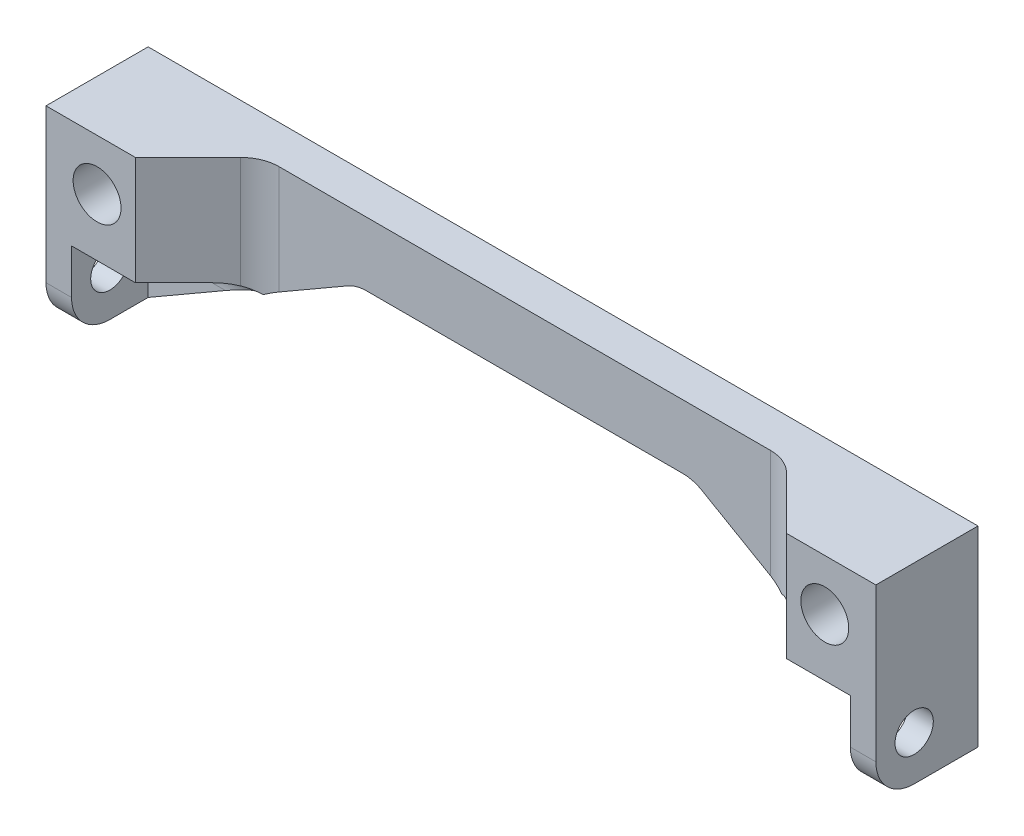
SolidWorks part; units mm, degrees
ref_plane "Front Plane" through (0, 0, 0) normal (0, 0, 1) x (1, 0, 0)
ref_plane "Top Plane" through (0, 0, 0) normal (0, 1, 0) x (1, 0, 0)
ref_plane "Right Plane" through (0, 0, 0) normal (1, 0, 0) x (0, 0, -1)
sketch "Sketch2" plane through (0, 0, 0) normal (0, 0, 1) x (1, 0, 0)
  line L0 (-65, 0) -> (65, 0)
  line L1 (65, 0) -> (65, -30)
  line L2 (65, -30) -> (61, -30)
  line L3 (61, -30) -> (26.359, -10)
  line L4 (26.359, -10) -> (-26.359, -10)
  line L5 (-26.359, -10) -> (-61, -30)
  line L6 (-61, -30) -> (-65, -30)
  line L7 (-65, -30) -> (-65, 0)
  circle A0 centre (-57, -8) radius 3.75
  circle A1 centre (57, -8) radius 3.75
  dimension "D6" = 7.5
  dimension "D1" = 30
  dimension "D2" = 130
  dimension "D3" = 4
  dimension "D4" = 10
  dimension "D5" = 30
  dimension "D7" = 8
  dimension "D8" = 8
  dimension "D9" = 8
  dimension "D10" = 30
extrude "Boss-Extrude1" add sketch "Sketch2" along normal blind 16
sketch "Sketch3" plane through (65, 0, 0) normal (1, 0, 0) x (0, 0, -1)
  line L0 (0, -30) -> (0, 0) construction
  line L1 (-16, -30) -> (0, -30) construction
  circle A0 centre (-10, -23) radius 3
  dimension "D2" = 6
  dimension "D1" = 7
  dimension "D3" = 10
extrude "Cut-Extrude1" cut sketch "Sketch3" against normal through all
sketch "Sketch4" plane through (0, 0, 0) normal (0, 1, 0) x (1, 0, 0)
  line L0 (-51, -16) -> (-41, -6)
  line L1 (65, -16) -> (-65, -16) construction
  line L2 (-41, -6) -> (41, -6)
  line L3 (41, -6) -> (51, -16)
  line L4 (51, -16) -> (-51, -16)
  line L5 (-65, -16) -> (-65, 0) construction
  line L6 (65, -16) -> (65, 0) construction
  line L7 (65, 0) -> (-65, 0) construction
  dimension "D1" = 14
  dimension "D2" = 14
  dimension "D3" = 6
  dimension "D4" = 45
extrude "Cut-Extrude2" cut sketch "Sketch4" against normal through all
sketch "Sketch5" plane through (-65, 0, 0) normal (-1, 0, 0) x (0, 0, 1)
  line L0 (4, -23) -> (4, -30)
  line L1 (16, -30) -> (0, -30) construction
  line L2 (4, -30) -> (16, -30)
  line L3 (16, -30) -> (16, -17)
  line L4 (16, 0) -> (16, -30) construction
  line L5 (16, -17) -> (10, -17)
  arc A0 (10, -17) -> (4, -23) centre (10, -23) ccw
  dimension "D1" = 12
extrude "Cut-Extrude3" cut sketch "Sketch5" against normal blind 30 from offset 4 offset against normal yes
sketch "Sketch6" plane through (65, 0, 0) normal (1, 0, 0) x (0, 0, -1)
  line L0 (-10, -17) -> (-16, -17)
  line L1 (-16, -17) -> (-16, -30)
  line L2 (-16, -30) -> (-4, -30)
  line L3 (-16, -30) -> (0, -30) construction
  line L4 (-4, -30) -> (-4, -23)
  arc A0 (-4, -23) -> (-10, -17) centre (-10, -23) ccw
  dimension "D1" = 12
extrude "Cut-Extrude4" cut sketch "Sketch6" against normal blind 30 from offset 4 offset against normal yes
fillet "Fillet1" radius 6 6 edges at (41, -9.2265, 6) (-41, -9.2265, 6) (-26.359, -10, 3) (26.359, -10, 3) (63, -30, 16) (-63, -30, 16)
